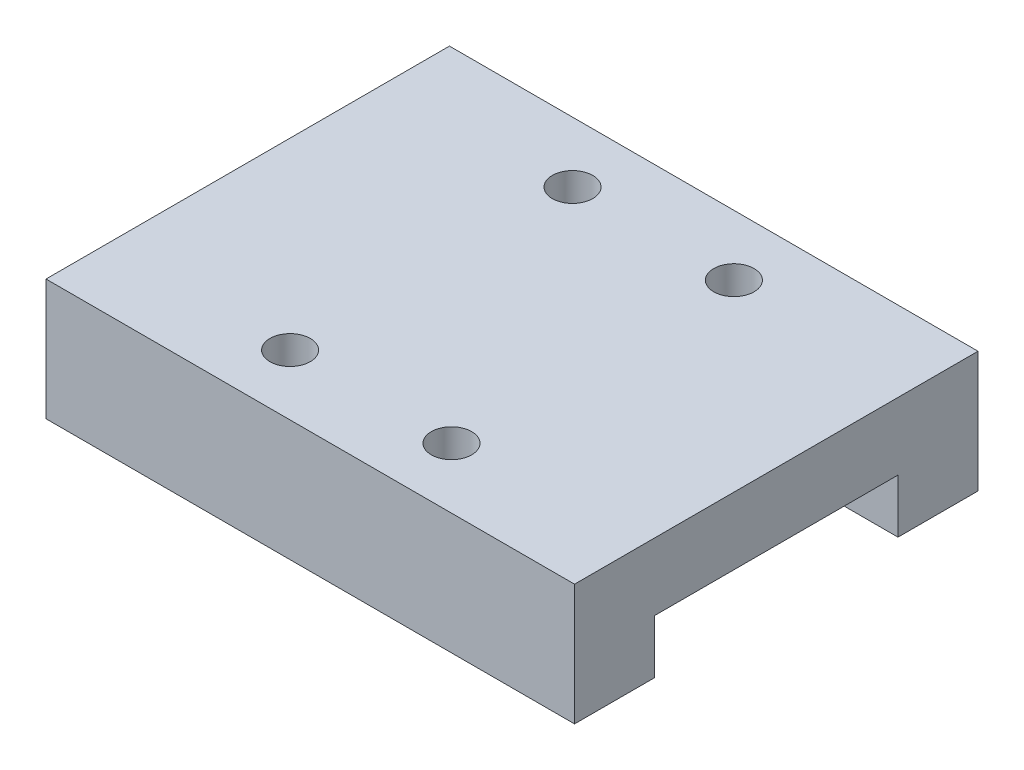
SolidWorks part; units mm, degrees
ref_plane "前视基准面" through (0, 0, 0) normal (0, 0, 1) x (1, 0, 0)
ref_plane "上视基准面" through (0, 0, 0) normal (0, 1, 0) x (1, 0, 0)
ref_plane "右视基准面" through (0, 0, 0) normal (1, 0, 0) x (0, 0, -1)
sketch "草图1" plane through (0, 0, 0) normal (0, 1, 0) x (1, 0, 0)
  line L1 (-19.65, 15) -> (19.65, 15)
  line L2 (-19.65, 15) -> (-19.65, -15)
  line L3 (-19.65, -15) -> (19.65, -15)
  line L4 (19.65, 15) -> (19.65, -15)
  line L5 (-19.65, 15) -> (19.65, -15) construction
  line L6 (-19.65, -15) -> (19.65, 15) construction
  point P0 (0, 0)
  dimension "D1" = 39.3
  dimension "D2" = 30
extrude "凸台-拉伸1" add sketch "草图1" along normal blind 9
sketch "草图2" plane through (0, 0, 0) normal (0, -1, 0) x (1, 0, 0)
  line L0 (-19.65, 9.05) -> (19.65, 9.05)
  line L1 (-19.65, -15) -> (-19.65, 15) construction
  line L2 (19.65, 15) -> (19.65, -15) construction
  line L3 (-19.65, -9.05) -> (19.65, -9.05)
  line L4 (-19.65, 9.05) -> (-19.65, -9.05)
  line L5 (19.65, 9.05) -> (19.65, -9.05)
  line L6 (0, 0) -> (20.595, 0) construction
  dimension "D1" = 18.1
  dimension "D2" = 9.05
extrude "切除-拉伸1" cut sketch "草图2" against normal blind 4
sketch "草图3" plane through (0, 9, 0) normal (0, 1, 0) x (1, 0, 0)
  line L0 (0, 0) -> (21.7618, 0) construction
  line L1 (0, 0) -> (0, 16.2929) construction
  circle A0 centre (-6, 10.5) radius 1.5
  circle A1 centre (6, 10.5) radius 1.5
  circle A2 centre (6, -10.5) radius 1.5
  circle A3 centre (-6, -10.5) radius 1.5
  dimension "D1" = 3
  dimension "D2" = 12
  dimension "D3" = 21
extrude "切除-拉伸2" cut sketch "草图3" against normal blind 5
